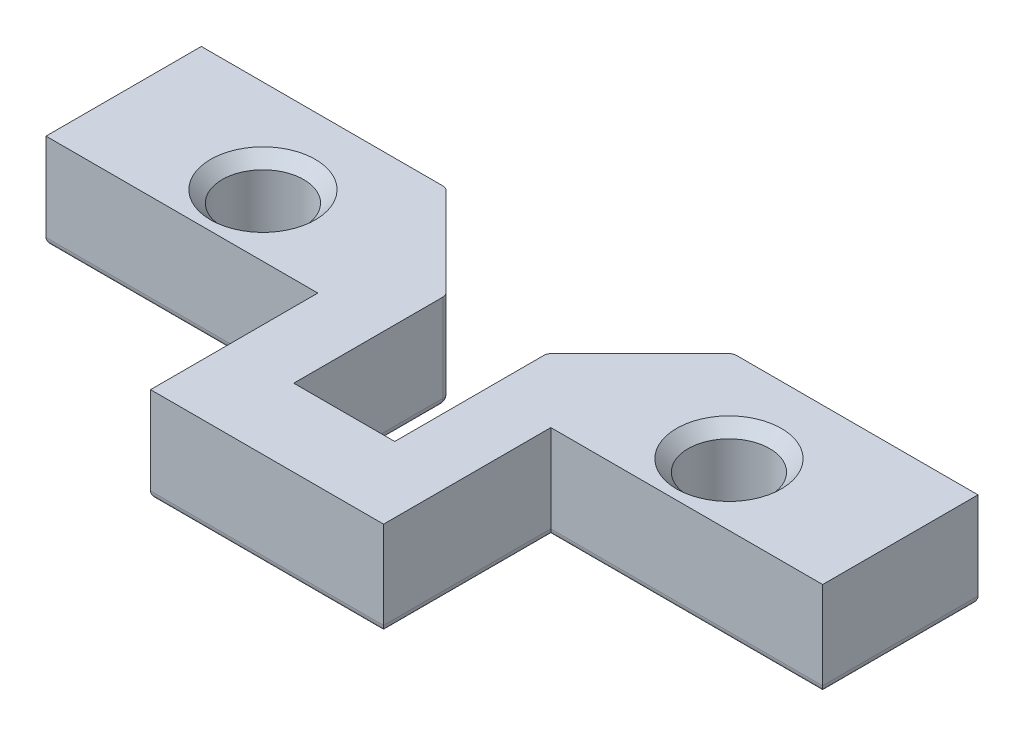
SolidWorks part; units mm, degrees
ref_plane "Front Plane" through (0, 0, 0) normal (0, 0, 1) x (1, 0, 0)
ref_plane "Top Plane" through (0, 0, 0) normal (0, 1, 0) x (1, 0, 0)
ref_plane "Right Plane" through (0, 0, 0) normal (1, 0, 0) x (0, 0, -1)
sketch "Sketch2" plane through (0, 0, 0) normal (0, 1, 0) x (1, 0, 0)
  line L1 (-50, -10) -> (50, -10)
  line L2 (-50, -10) -> (-50, 10)
  line L3 (-50, 10) -> (50, 10)
  line L4 (50, -10) -> (50, 10)
  line L5 (-50, -10) -> (50, 10) construction
  line L6 (-50, 10) -> (50, -10) construction
  line L7 (15, -10) -> (-15, -10)
  line L8 (15, -10) -> (15, -31.5374)
  line L9 (15, -31.5374) -> (-15, -31.5374)
  line L10 (-15, -10) -> (-15, -31.5374)
  line L11 (-6.5, 10) -> (6.5, 10)
  line L12 (-6.5, 10) -> (-6.5, -21.6)
  line L13 (-6.5, -21.6) -> (6.5, -21.6)
  line L14 (6.5, 10) -> (6.5, -21.6)
  circle A0 centre (-30.0667, -2) radius 5.25
  circle A1 centre (29.9333, -2) radius 5.25
  point P0 (0, 0)
  dimension "D9" = 60
  dimension "D12" = 10.5
  dimension "D13" = 10.5
  dimension "D1" = 20
  dimension "D2" = 100
  dimension "D3" = 35
  dimension "D4" = 35
  dimension "D5" = 41.5374
  dimension "D6" = 31.6
  dimension "D7" = 13
  dimension "D8" = 6.5
  dimension "D10" = 30
  dimension "D11" = 12
extrude "Boss-Extrude1" add sketch "Sketch2" along normal blind 12.3 contours L12 L3 L2 L1 A0 | L1 L14 L13 L12 L10 L9 L8 | L3 L14 L1 L4 A1
chamfer "Chamfer1" distance 1.5 angle 45 2 edges at (29.9333, 12.3, 7.25) (-30.0667, 12.3, 7.25)
chamfer "Chamfer2" distance 12 angle 45 2 edges at (6.5, 6.15, -10) (-6.5, 6.15, -10)
fillet "Fillet1" radius 1 17 edges at (12.5, 0, -4) (-12.5, 0, -4) (-34.25, 0, -10) (-50, 0, 0) (32.5, 0, 10) (-15, 0, 20.7687) (0, 0, 31.5374) (15, 0, 20.7687) (-32.5, 0, 10) (-18.5, 6.15, -10) (-6.5, 6.15, 2) (6.5, 6.15, 2) (18.5, 6.15, -10) (50, 0, 0) (34.25, 0, -10) (6.5, 0, 11.8) (-6.5, 0, 11.8)
